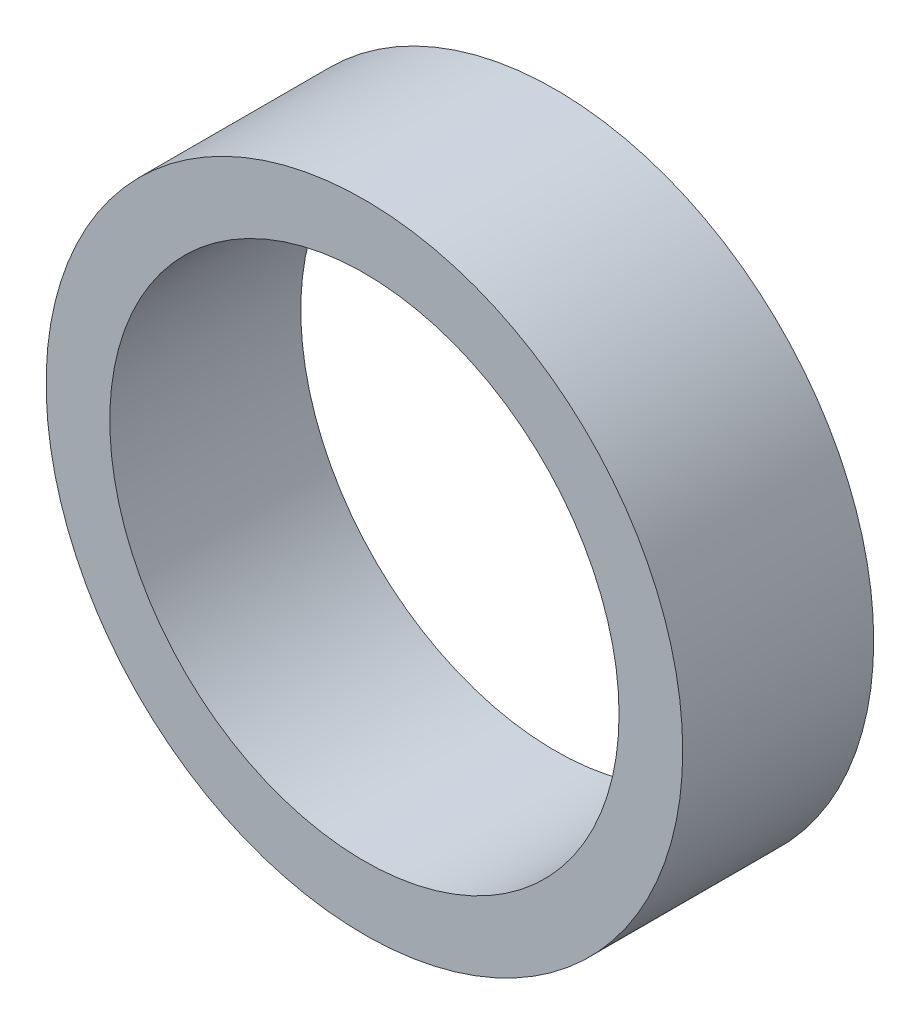
SolidWorks part; units mm, degrees
ref_plane "Front Plane" through (0, 0, 0) normal (0, 0, 1) x (1, 0, 0)
ref_plane "Top Plane" through (0, 0, 0) normal (0, 1, 0) x (1, 0, 0)
ref_plane "Right Plane" through (0, 0, 0) normal (1, 0, 0) x (0, 0, -1)
sketch "Sketch1" plane through (0, 0, 0) normal (0, 0, 1) x (1, 0, 0)
  circle A0 centre (0, 0) radius 20
  circle A1 centre (0, 0) radius 25
  dimension "D1" = 40
  dimension "D2" = 50
extrude "Boss-Extrude1" add sketch "Sketch1" along normal blind 15
